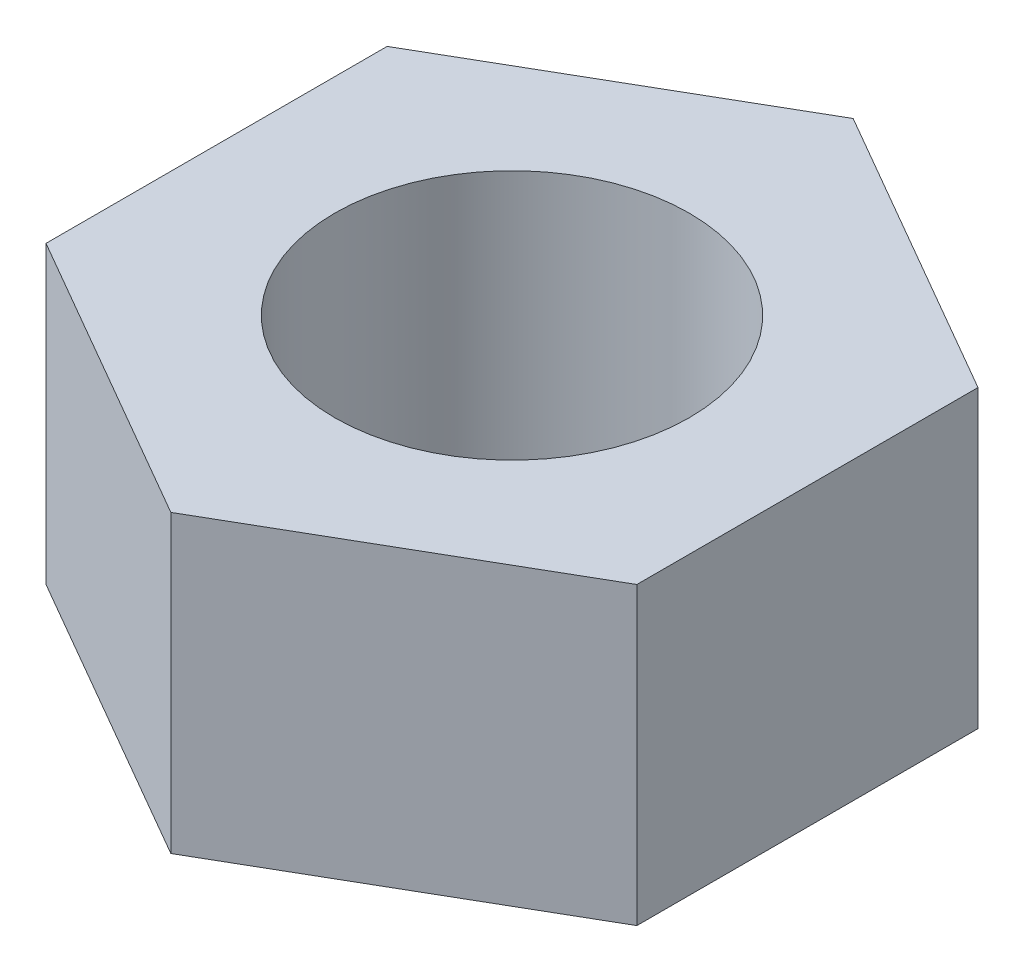
SolidWorks part; units mm, degrees
ref_plane "Plan de face" through (0, 0, 0) normal (0, 0, 1) x (1, 0, 0)
ref_plane "Plan de dessus" through (0, 0, 0) normal (0, 1, 0) x (1, 0, 0)
ref_plane "Plan de droite" through (0, 0, 0) normal (1, 0, 0) x (0, 0, -1)
sketch "Esquisse1" plane through (0, 0, 0) normal (0, 1, 0) x (1, 0, 0)
  line L0 (-5, 2.8868) -> (0, 5.7735)
  line L1 (-5, 2.8868) -> (5, 2.8868) construction
  line L2 (-5, 2.8868) -> (-5, -2.8868)
  line L3 (-5, -2.8868) -> (5, -2.8868) construction
  line L4 (5, 2.8868) -> (5, -2.8868)
  line L5 (-5, 2.8868) -> (5, -2.8868) construction
  line L6 (-5, -2.8868) -> (5, 2.8868) construction
  line L7 (0, 5.7735) -> (5, 2.8868)
  line L8 (-5, -2.8868) -> (0, -5.7735)
  line L9 (0, -5.7735) -> (5, -2.8868)
  circle A0 centre (0, 0) radius 3
  dimension "D3" = 6
  dimension "D1" = 120
  dimension "D2" = 10
extrude "Boss.-Extru.1" add sketch "Esquisse1" along normal blind 5
